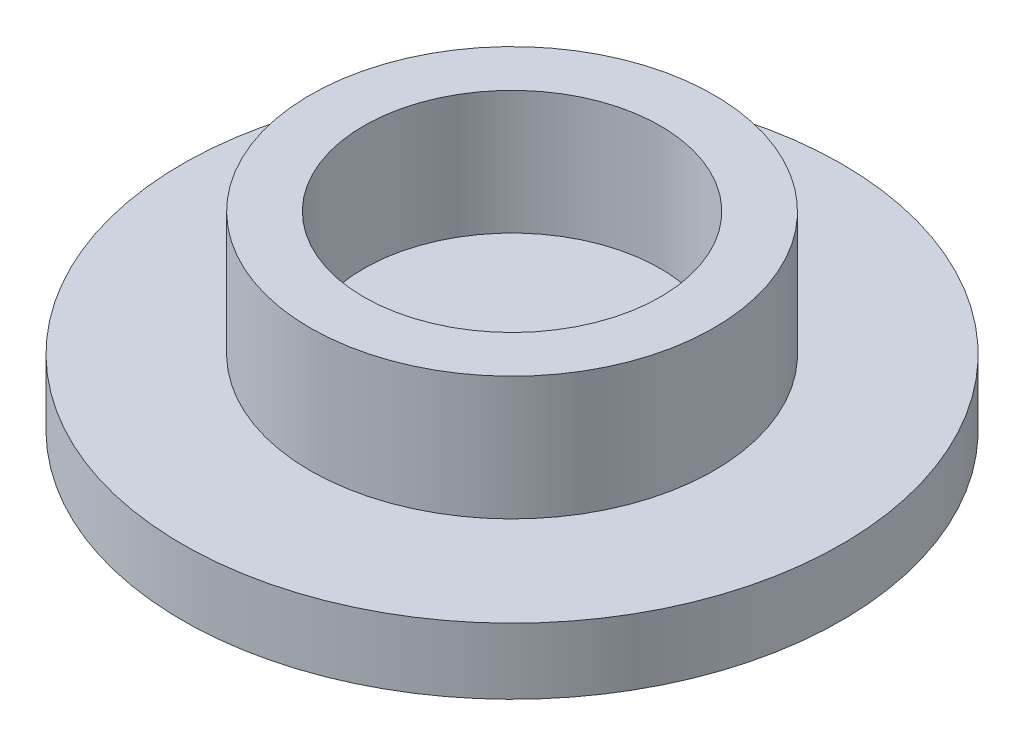
SolidWorks part; units mm, degrees
ref_plane "Front Plane" through (0, 0, 0) normal (0, 0, 1) x (1, 0, 0)
ref_plane "Top Plane" through (0, 0, 0) normal (0, 1, 0) x (1, 0, 0)
ref_plane "Right Plane" through (0, 0, 0) normal (1, 0, 0) x (0, 0, -1)
sketch "Sketch1" plane through (0, 0, 0) normal (0, 1, 0) x (1, 0, 0)
  circle A0 centre (0, 0) radius 1.8
  circle A1 centre (0, 0) radius 2.45
  dimension "D1" = 3.6
  dimension "D2" = 4.9
extrude "Boss-Extrude1" add sketch "Sketch1" along normal blind 1.5
sketch "Sketch2" plane through (0, 0, 0) normal (0, -1, 0) x (1, 0, 0)
  circle A0 centre (0, 0) radius 4
  dimension "D1" = 8
extrude "Boss-Extrude2" add sketch "Sketch2" along normal blind 0.8
